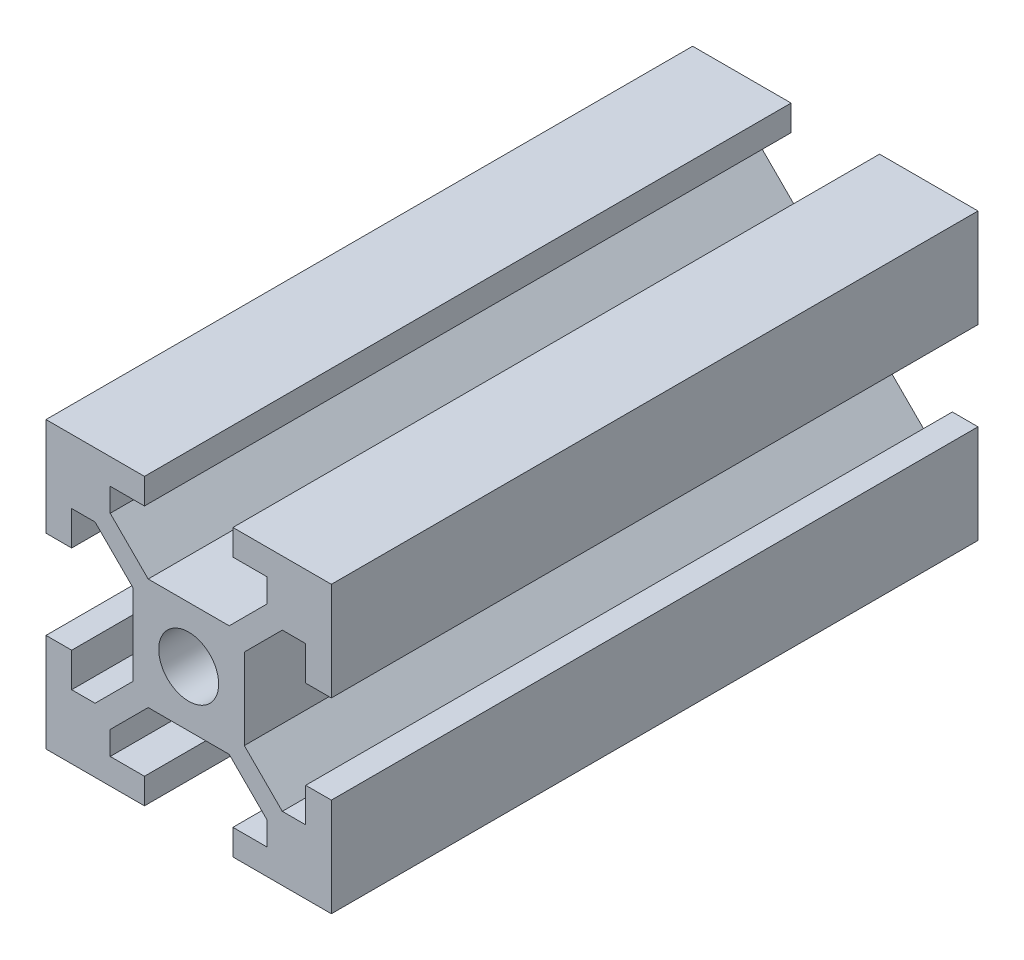
SolidWorks part; units mm, degrees
ref_plane "Front Plane" through (0, 0, 0) normal (0, 0, 1) x (1, 0, 0)
ref_plane "Top Plane" through (0, 0, 0) normal (0, 1, 0) x (1, 0, 0)
ref_plane "Right Plane" through (0, 0, 0) normal (1, 0, 0) x (0, 0, -1)
sketch "Sketch1" plane through (0, 0, 0) normal (0, 0, 1) x (1, 0, 0)
  line L0 (-3.1, 10) -> (-3.1, 8.2007)
  line L1 (-10, 10) -> (-3.1, 10)
  line L2 (-10, 10) -> (-10, 3.1)
  line L3 (-10, -10) -> (-3.1, -10)
  line L4 (10, 10) -> (10, 3.1)
  line L5 (-10, 10) -> (10, -10) construction
  line L6 (-10, -10) -> (10, 10) construction
  line L7 (-3.1, 8.2007) -> (-5.5, 8.2007)
  line L8 (-5.5, 8.2007) -> (-5.5, 6.5607)
  line L9 (-5.5, 6.5607) -> (-2.84, 3.9007)
  line L10 (-2.84, 3.9007) -> (2.84, 3.9007)
  line L11 (2.84, 3.9007) -> (5.5, 6.5607)
  line L12 (5.5, 6.5607) -> (5.5, 8.2007)
  line L13 (5.5, 8.2007) -> (3.1, 8.2007)
  line L14 (3.1, 8.2007) -> (3.1, 10)
  line L15 (-3.1, 8.2007) -> (3.1, 8.2007) construction
  line L16 (-5.5, 6.5607) -> (5.5, 6.5607) construction
  line L17 (3.1, 10) -> (10, 10)
  line L18 (8.2007, 3.1) -> (8.2007, 5.5)
  line L19 (8.2007, 5.5) -> (6.5607, 5.5)
  line L20 (6.5607, 5.5) -> (3.9007, 2.84)
  line L21 (3.9007, 2.84) -> (3.9007, -2.84)
  line L22 (3.9007, -2.84) -> (6.5607, -5.5)
  line L23 (6.5607, -5.5) -> (8.2007, -5.5)
  line L24 (8.2007, -5.5) -> (8.2007, -3.1)
  line L25 (8.2007, 3.1) -> (8.2007, -3.1) construction
  line L26 (6.5607, 5.5) -> (6.5607, -5.5) construction
  line L27 (10, 3.1) -> (8.2007, 3.1)
  line L28 (8.2007, -3.1) -> (10, -3.1)
  line L29 (3.1, -8.2007) -> (5.5, -8.2007)
  line L30 (5.5, -8.2007) -> (5.5, -6.5607)
  line L31 (5.5, -6.5607) -> (2.84, -3.9007)
  line L32 (2.84, -3.9007) -> (-2.84, -3.9007)
  line L33 (-2.84, -3.9007) -> (-5.5, -6.5607)
  line L34 (-5.5, -6.5607) -> (-5.5, -8.2007)
  line L35 (-5.5, -8.2007) -> (-3.1, -8.2007)
  line L36 (3.1, -8.2007) -> (-3.1, -8.2007) construction
  line L37 (5.5, -6.5607) -> (-5.5, -6.5607) construction
  line L38 (3.1, -10) -> (3.1, -8.2007)
  line L39 (-3.1, -8.2007) -> (-3.1, -10)
  line L40 (-8.2007, -3.1) -> (-8.2007, -5.5)
  line L41 (-8.2007, -5.5) -> (-6.5607, -5.5)
  line L42 (-6.5607, -5.5) -> (-3.9007, -2.84)
  line L43 (-3.9007, -2.84) -> (-3.9007, 2.84)
  line L44 (-3.9007, 2.84) -> (-6.5607, 5.5)
  line L45 (-6.5607, 5.5) -> (-8.2007, 5.5)
  line L46 (-8.2007, 5.5) -> (-8.2007, 3.1)
  line L47 (-8.2007, -3.1) -> (-8.2007, 3.1) construction
  line L48 (-6.5607, -5.5) -> (-6.5607, 5.5) construction
  line L49 (-10, -3.1) -> (-8.2007, -3.1)
  line L50 (-8.2007, 3.1) -> (-10, 3.1)
  line L51 (10, -3.1) -> (10, -10)
  line L52 (3.1, -10) -> (10, -10)
  line L53 (-10, -3.1) -> (-10, -10)
  point P0 (0, 0)
  point P8 (0, 8.2007)
  point P18 (0, 3.9007)
  dimension "D1" = 20
  dimension "D2" = 20
  dimension "D3" = 5.68
  dimension "D4" = 6.2
  dimension "D5" = 4.3
  dimension "D6" = 11
  dimension "D7" = 0.75
  dimension "D8" = 4
extrude "Boss-Extrude1" add sketch "Sketch1" along normal blind 45.32
sketch "Sketch2" plane through (0, 0, 45.32) normal (0, 0, 1) x (1, 0, 0)
  circle A0 centre (0, 0) radius 2.1
  dimension "D1" = 4.2
extrude "Cut-Extrude1" cut sketch "Sketch2" against normal through all
sketch "Sketch3" plane through (0, 3.9007, 0) normal (0, 1, 0) x (1, 0, 0)
  line L0 (0, 0) -> (0, -45.32) construction
  line L1 (2.84, -45.32) -> (-2.84, -45.32) construction
  circle A0 centre (0, -22.66) radius 2.1
  dimension "D1" = 4.2
extrude "Cut-Extrude2" cut sketch "Sketch3" against normal through all
